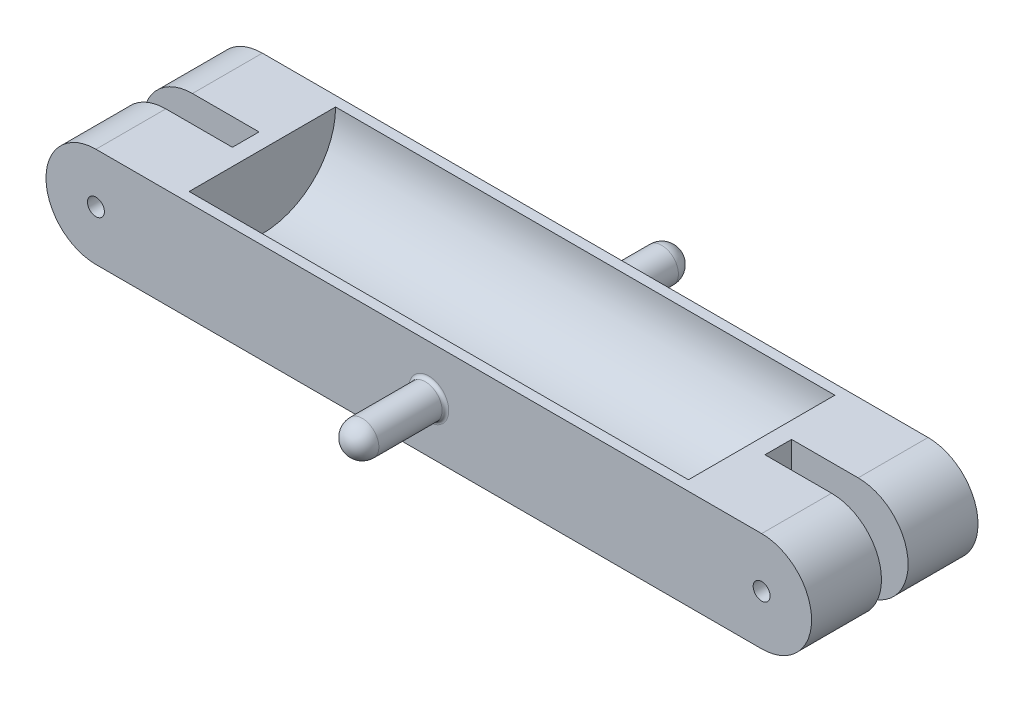
SolidWorks part; units mm, degrees
ref_plane "Front Plane" through (0, 0, 0) normal (0, 0, 1) x (1, 0, 0)
ref_plane "Top Plane" through (0, 0, 0) normal (0, 1, 0) x (1, 0, 0)
ref_plane "Right Plane" through (0, 0, 0) normal (1, 0, 0) x (0, 0, -1)
sketch "Sketch2" plane through (0, 0, 0) normal (0, 0, 1) x (1, 0, 0)
  line L0 (0, 15) -> (100, 15)
  line L1 (100, -15) -> (0, -15)
  line L2 (0, -15) -> (0, 15)
  line L3 (100, 0) -> (0, 0) construction
  arc A2 (100, -15) -> (100, 15) centre (100, 0) ccw
  circle A3 centre (100, 0) radius 2.55
  dimension "D2" = 5.1
  dimension "D3" = 15
  dimension "D1" = 100
extrude "Boss-Extrude1" add sketch "Sketch2" along normal blind 50 contours L0 A2 L1 L2 | A3
sketch "Sketch6" plane through (0, 15, 0) normal (0, 1, 0) x (1, 0, 0)
  line L0 (0, -25) -> (80, -25) construction
  line L1 (0, -50) -> (0, 0) construction
  line L2 (80, -25) -> (115, -25) construction
  line L4 (115, -50) -> (115, 0) construction
  line L6 (80, -29) -> (115, -29)
  line L7 (80, -29) -> (80, -21)
  line L8 (80, -21) -> (115, -21)
  line L9 (115, -29) -> (115, -21)
  line L10 (97.5, -21) -> (97.5, -29) construction
  line L11 (80, -25) -> (115, -25) construction
  point P263 (97.5, -25)
  dimension "D1" = 35
  dimension "D2" = 8
extrude "Cut-Extrude3" cut sketch "Sketch6" along direction (0, -1, 0) on the side against the normal through all
sketch "Sketch7" plane through (0, 0, 0) normal (-1, 0, 0) x (0, 0, 1)
  line L1 (50, 15) -> (0, 15) construction
  line L3 (3, 15) -> (47, 15)
  arc A0 (3, 15) -> (47, 15) centre (25, 15) ccw
  dimension "D1" = 22
extrude "Cut-Extrude6" cut sketch "Sketch7" against normal blind 75
mirror "Mirror3" about plane through (0, -15, 50) normal (-1, 0, 0) of "Cut-Extrude3", "Boss-Extrude1", "Cut-Extrude6"
sketch "Sketch9" plane through (0, 0, 50) normal (0, 0, 1) x (1, 0, 0)
  circle A0 centre (0, 0) radius 5
  dimension "D1" = 10
extrude "Boss-Extrude2" add sketch "Sketch9" along normal blind 20
sketch "Sketch12" plane through (0, 0, 70) normal (0, 0, 1) x (1, 0, 0)
  line L0 (-5, 0) -> (5, 0) construction
  line L1 (0, -5) -> (0, 5)
  arc A0 (0, -5) -> (0, 5) centre (0, 0) ccw
  circle A3 centre (0, 0) radius 5 construction
revolve "Revolve1" add sketch "Sketch12" angle 180 about L1
ref_plane "Plane1" through (75, -7, 25) normal (0, 0, 1) x (1, 0, 0)
mirror "Mirror4" about plane through (75, -7, 25) normal (0, 0, 1) of "Revolve1", "Boss-Extrude2"
fillet "Fillet2" radius 1 2 edges at (5, 0, 50) (5, 0, 0)
